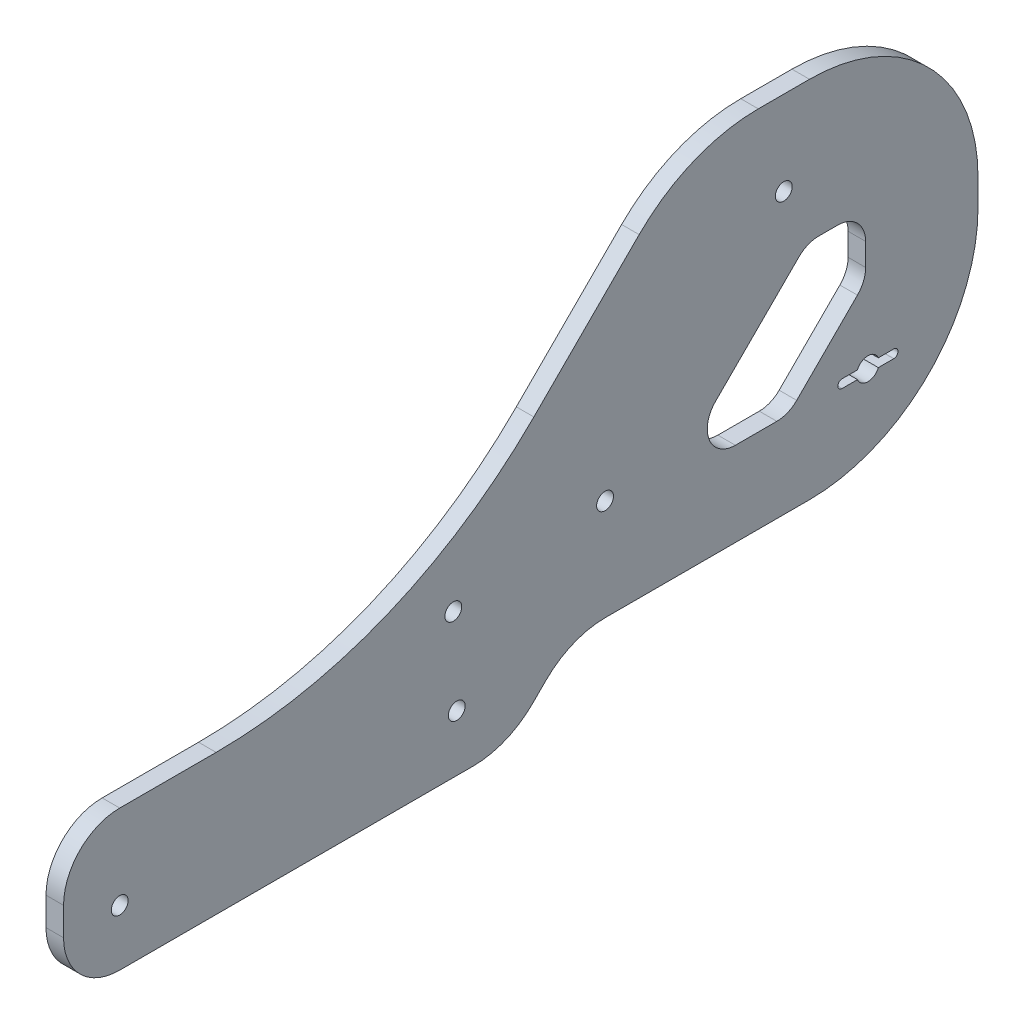
SolidWorks part; units mm, degrees
ref_plane "Front Plane" through (0, 0, 0) normal (0, 0, 1) x (1, 0, 0)
ref_plane "Top Plane" through (0, 0, 0) normal (0, 1, 0) x (1, 0, 0)
ref_plane "Right Plane" through (0, 0, 0) normal (1, 0, 0) x (0, 0, -1)
sketch "Sketch1" plane through (0, 0, 0) normal (1, 0, 0) x (0, 0, -1)
  line L0 (-62.0729, -10) -> (29.851, 81.9239) construction
  line L1 (29.851, 81.9239) -> (22.0729, 89.7021) construction
  line L2 (22.0729, 89.7021) -> (-69.851, -2.2218) construction
  line L3 (-69.851, -2.2218) -> (-62.0729, -10) construction
  line L4 (-4.6, 0) -> (4.6, 0) construction
  line L5 (-6, 5) -> (-6, -5) construction
  line L6 (-4.6, 0.75) -> (-1.854, 0.75)
  line L7 (-4.6, -0.75) -> (-1.854, -0.75)
  line L8 (-6, -5) -> (6, -5) construction
  line L9 (1.854, 0.75) -> (4.6, 0.75)
  line L10 (1.854, -0.75) -> (4.6, -0.75)
  line L11 (6, -5) -> (6, 5) construction
  line L12 (6, 5) -> (-6, 5) construction
  line L13 (-6, 5) -> (6, -5) construction
  line L14 (-69.851, -2.2218) -> (29.851, 81.9239) construction
  line L15 (-20, 39.851) -> (-20, 79.8794) construction
  line L16 (-9.747, 57.8823) -> (-1.9688, 50.1041) construction
  line L17 (-46.7993, 3.0108) -> (-14.9795, 34.8306) construction
  line L18 (-73.2042, -16.1314) -> (-133.2042, -16.1314) construction
  line L19 (-73.8108, -0.5248) -> (-63.2042, -11.1314) construction
  line L20 (-62.0729, -10) -> (-63.2042, -11.1314) construction
  line L21 (-143.2042, -1.1314) -> (-143.2042, -26.1314)
  line L22 (-143.2042, -26.1314) -> (-64.0621, -26.1314)
  line L23 (-64.0621, -26.1314) -> (-52.9307, -15)
  line L24 (-52.9307, -15) -> (19.6, -15)
  line L25 (19.6, -15) -> (19.6, 49.8306)
  line L26 (19.6, 49.8306) -> (-31.9408, 49.8306)
  line L27 (-31.9408, 49.8306) -> (-82.9027, -1.1314)
  line L28 (-82.9027, -1.1314) -> (-143.2042, -1.1314)
  line L29 (0, -31) -> (-153.4899, -31) construction
  line L30 (-35.668, 0) -> (-10.8374, 24.8306)
  line L31 (-10.8374, 24.8306) -> (-0.4, 24.8306)
  line L32 (-0.4, 24.8306) -> (-0.4, 13.7421)
  line L33 (-0.4, 13.7421) -> (-14.1421, 0)
  line L34 (-14.1421, 0) -> (-35.668, 0)
  arc A0 (-1.854, -0.75) -> (1.854, -0.75) centre (0, 0) ccw
  arc A1 (-4.6, 0.75) -> (-4.6, -0.75) centre (-4.6, 0) ccw
  arc A2 (1.854, 0.75) -> (-1.854, 0.75) centre (0, 0) ccw
  circle A3 centre (0, 0) radius 31 construction
  arc A4 (4.6, -0.75) -> (4.6, 0.75) centre (4.6, 0) ccw
  circle A5 centre (-46.7993, 3.0108) radius 1.5
  circle A6 centre (-14.9795, 34.8306) radius 1.5
  circle A7 centre (-73.8108, -0.5248) radius 1.5
  circle A8 centre (-73.2042, -16.1314) radius 1.5
  circle A9 centre (-133.2042, -16.1314) radius 1.5
  point P11 (-4.6, 0)
  point P16 (4.6, 0)
  dimension "D4" = 4
  dimension "D5" = 0.75
  dimension "D9" = 62
  dimension "D14" = 3
  dimension "D15" = 1.6
  dimension "D1" = 11
  dimension "D2" = 130
  dimension "D3" = 9.2
  dimension "D6" = 10
  dimension "D7" = 12
  dimension "D8" = 45
  dimension "D10" = 20
  dimension "D11" = 10
  dimension "D12" = 45
  dimension "D13" = 1.6
  dimension "D16" = 20
  dimension "D17" = 65
  dimension "D18" = 15
  dimension "D19" = 5
  dimension "D20" = 10
  dimension "D21" = 60
  dimension "D22" = 10
  dimension "D23" = 15
  dimension "D24" = 10
  dimension "D25" = 15
  dimension "D26" = 10
  dimension "D27" = 15
  dimension "D28" = 15
  dimension "D29" = 10
  dimension "D30" = 45
  dimension "D31" = 10
  dimension "D32" = 10
  dimension "D33" = 15
  dimension "D34" = 20
  dimension "D35" = 25
extrude "Boss-Extrude1" add sketch "Sketch1" along normal blind 3.125
fillet "Fillet1" radius 10 2 edges at (1.5625, -1.1314, 143.2042) (1.5625, -26.1314, 143.2042)
fillet "Fillet2" radius 15 2 edges at (1.5625, -26.1314, 64.0621) (1.5625, -15, 52.9307)
fillet "Fillet3" radius 30 1 edges at (1.5625, -15, -19.6)
fillet "Fillet4" radius 30 1 edges at (1.5625, 49.8306, 31.9408)
fillet "Fillet5" radius 80 1 edges at (1.5625, -1.1314, 82.9027)
fillet "Fillet6" radius 30 1 edges at (1.5625, 49.8306, -19.6)
fillet "Fillet7" radius 5 5 edges at (1.5625, 0, 35.668) (1.5625, 24.8306, 10.8374) (1.5625, 24.8306, 0.4) (1.5625, 13.7421, 0.4) (1.5625, 0, 14.1421)
